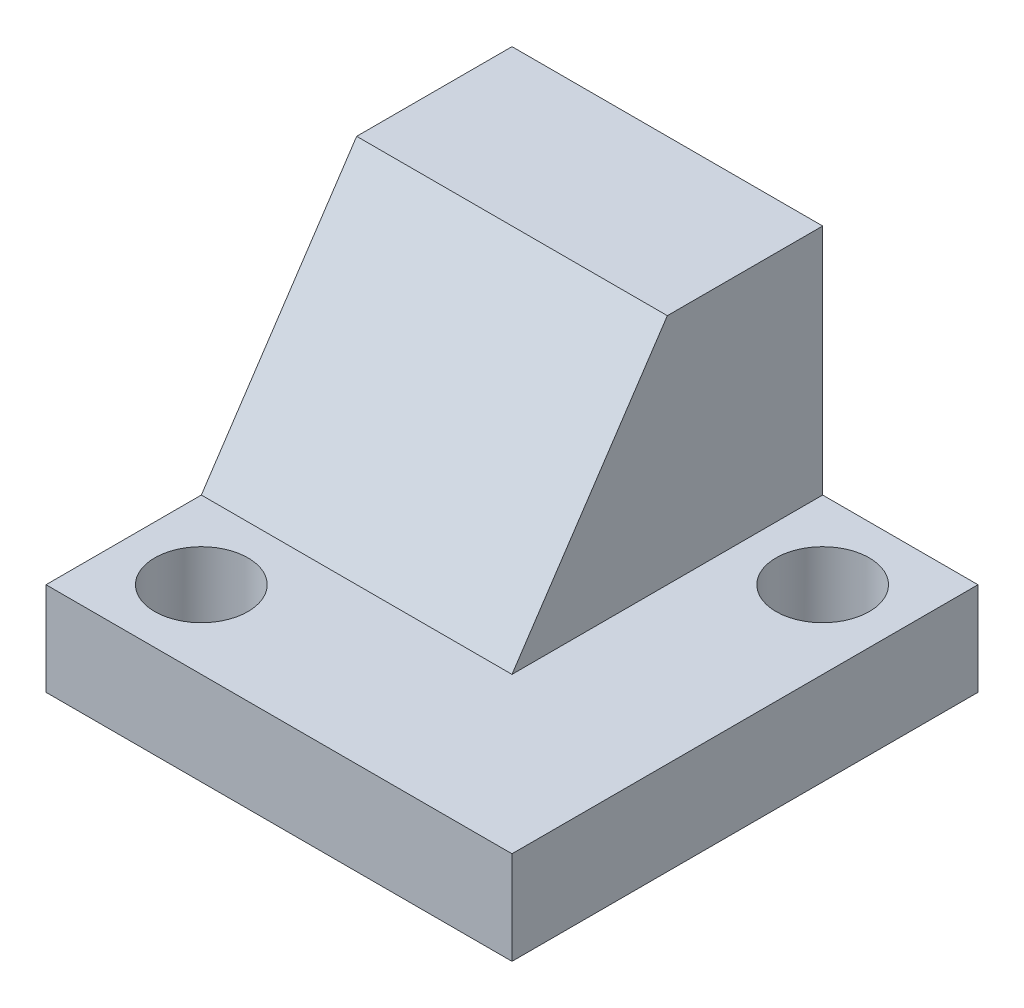
SolidWorks part; units mm, degrees
ref_plane "Front Plane" through (0, 0, 0) normal (0, 0, 1) x (1, 0, 0)
ref_plane "Top Plane" through (0, 0, 0) normal (0, 1, 0) x (1, 0, 0)
ref_plane "Right Plane" through (0, 0, 0) normal (1, 0, 0) x (0, 0, -1)
sketch "Sketch1" plane through (0, 0, 0) normal (0, 1, 0) x (1, 0, 0)
  line L1 (-19.05, -19.05) -> (19.05, -19.05)
  line L2 (-19.05, -19.05) -> (-19.05, 19.05)
  line L3 (-19.05, 19.05) -> (19.05, 19.05)
  line L4 (19.05, -19.05) -> (19.05, 19.05)
  line L5 (-19.05, -19.05) -> (19.05, 19.05) construction
  line L6 (-19.05, 19.05) -> (19.05, -19.05) construction
  point P0 (0, 0)
  dimension "D1" = 38.1
  dimension "D2" = 38.1
extrude "Boss-Extrude1" add sketch "Sketch1" along normal blind 7.62
sketch "Sketch2" plane through (0, 7.62, 0) normal (0, 1, 0) x (1, 0, 0)
  line L1 (6.35, -6.35) -> (-19.05, -6.35)
  line L2 (6.35, -6.35) -> (6.35, 19.05)
  line L3 (6.35, 19.05) -> (-19.05, 19.05)
  line L4 (-19.05, -6.35) -> (-19.05, 19.05)
  line L5 (6.35, -6.35) -> (-19.05, 19.05) construction
  line L6 (6.35, 19.05) -> (-19.05, -6.35) construction
  point P0 (-6.35, 6.35)
  dimension "D1" = 25.4
  dimension "D2" = 25.4
extrude "Boss-Extrude2" add sketch "Sketch2" along normal blind 19.05
sketch "Sketch3" plane through (0, 7.62, 0) normal (0, 1, 0) x (1, 0, 0)
  line L0 (12.7, 12.7) -> (-12.7, 12.7) construction
  line L1 (-12.7, 12.7) -> (-12.7, -12.7) construction
  line L2 (-12.7, -12.7) -> (-19.05, -12.7) construction
  line L3 (-19.05, -6.35) -> (-19.05, -19.05) construction
  line L4 (12.7, 12.7) -> (19.05, 12.7) construction
  line L5 (19.05, -19.05) -> (19.05, 19.05) construction
  line L6 (12.7, 12.7) -> (12.7, 19.05) construction
  line L9 (-12.7, -12.7) -> (-12.7, -19.05) construction
  line L10 (-19.05, -19.05) -> (19.05, -19.05) construction
  line L11 (19.05, 19.05) -> (6.35, 19.05) construction
  circle A0 centre (12.7, 12.7) radius 3.81
  circle A1 centre (-12.7, -12.7) radius 3.81
  point P4 (0, 0)
  dimension "D3" = 7.62
  dimension "D1" = 25.4
  dimension "D2" = 25.4
extrude "Cut-Extrude1" cut sketch "Sketch3" against normal up to next
sketch "Sketch4" plane through (-19.05, 0, 0) normal (-1, 0, 0) x (0, 0, 1)
  line L0 (-13.335, 21.59) -> (-10.541, 21.59)
  line L1 (-10.541, 21.59) -> (-10.541, 10.414)
  line L2 (-10.541, 10.414) -> (0.635, 10.414)
  line L3 (0.635, 10.414) -> (0.635, 7.62)
  line L4 (0.635, 7.62) -> (-13.335, 7.62)
  line L5 (-13.335, 7.62) -> (-13.335, 21.59)
  line L6 (6.35, 7.62) -> (-19.05, 7.62) construction
  line L7 (6.35, 7.62) -> (19.05, 7.62) construction
  point P3 (-6.35, 7.62)
  point P5 (-6.35, 7.62)
  point P8 (0, 0)
  dimension "D1" = 2.794
  dimension "D2" = 13.97
extrude "Cut-Extrude2" cut sketch "Sketch4" against normal blind 6.35
sketch "Sketch5" plane through (-19.05, 0, 0) normal (-1, 0, 0) x (0, 0, 1)
  line L0 (-6.35, 26.67) -> (6.35, 7.62)
  line L1 (-19.05, 26.67) -> (6.35, 26.67) construction
  line L2 (6.35, 26.67) -> (6.35, 7.62) construction
  line L3 (6.35, 7.62) -> (6.35, 26.67)
  line L4 (6.35, 26.67) -> (-6.35, 26.67)
  point P6 (6.35, 7.62)
extrude "Cut-Extrude3" cut sketch "Sketch5" against normal up to next
